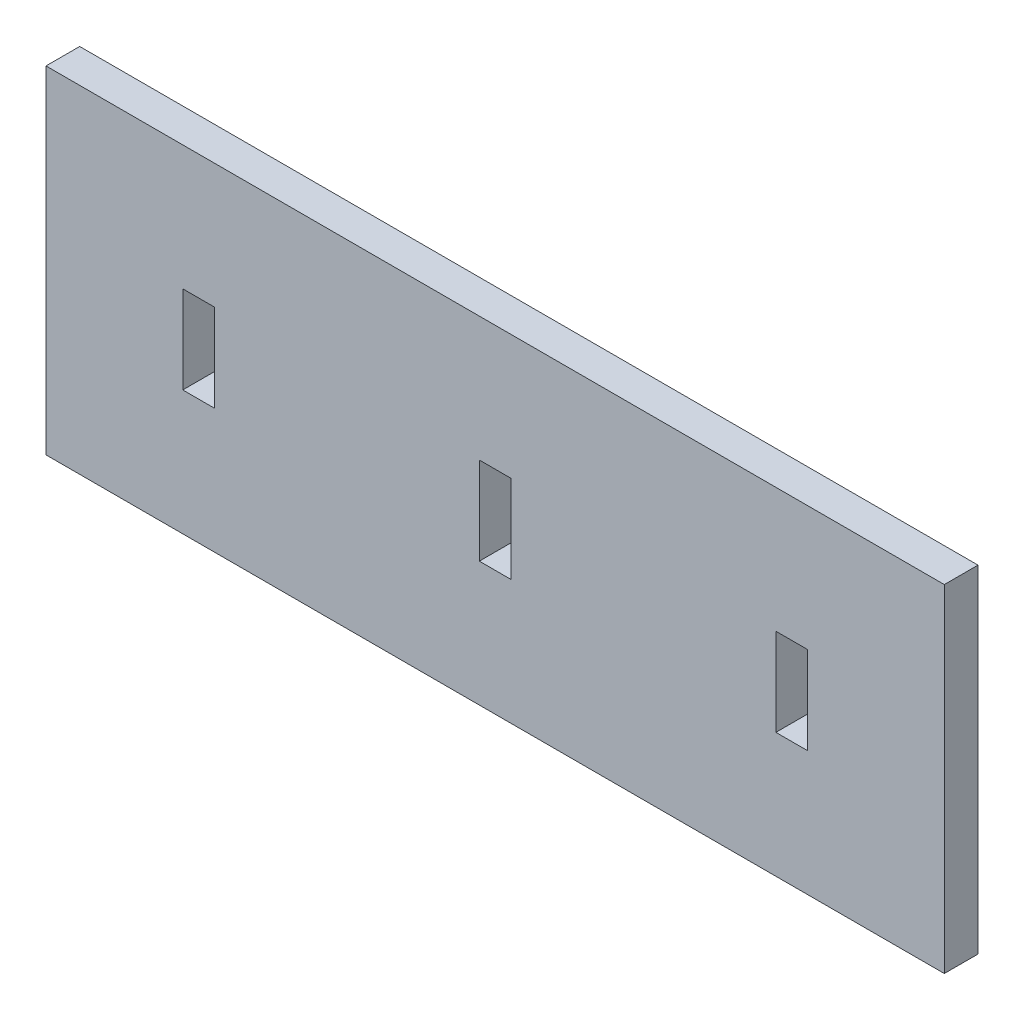
SolidWorks part; units mm, degrees
ref_plane "Front Plane" through (0, 0, 0) normal (0, 0, 1) x (1, 0, 0)
ref_plane "Top Plane" through (0, 0, 0) normal (0, 1, 0) x (1, 0, 0)
ref_plane "Right Plane" through (0, 0, 0) normal (1, 0, 0) x (0, 0, -1)
sketch "Sketch2" plane through (0, 0, 0) normal (0, 0, 1) x (1, 0, 0)
  line L0 (-26.41, 3.9) -> (26.41, 3.9) construction
  line L1 (-40, -15) -> (40, -15)
  line L2 (-40, -15) -> (-40, 15)
  line L3 (-40, 15) -> (40, 15)
  line L4 (40, -15) -> (40, 15)
  line L5 (-27.82, 3.9) -> (-25, 3.9)
  line L6 (-27.82, 3.9) -> (-27.82, -3.9)
  line L7 (-27.82, -3.9) -> (-25, -3.9)
  line L8 (-25, 3.9) -> (-25, -3.9)
  line L9 (25, 3.9) -> (27.82, 3.9)
  line L10 (25, 3.9) -> (25, -3.9)
  line L11 (25, -3.9) -> (27.82, -3.9)
  line L12 (27.82, 3.9) -> (27.82, -3.9)
  line L13 (-1.41, -3.9) -> (1.41, -3.9)
  line L14 (-1.41, -3.9) -> (-1.41, 3.9)
  line L15 (-1.41, 3.9) -> (1.41, 3.9)
  line L16 (1.41, -3.9) -> (1.41, 3.9)
  line L17 (-1.41, -3.9) -> (1.41, 3.9) construction
  line L18 (-1.41, 3.9) -> (1.41, -3.9) construction
  point P0 (0, 0)
  point P14 (0, -15)
  point P15 (40, 0)
  point P16 (25, 0)
  point P17 (-25, 0)
  point P18 (0, 0)
  point P25 (0, 3.9)
  point P26 (1.41, 3.4198)
  point P27 (25, 3.9)
  point P28 (26.41, 3.9)
  dimension "D1" = 2.82
  dimension "D2" = 80
  dimension "D3" = 30
  dimension "D4" = 7.8
  dimension "D5" = 50
extrude "Boss-Extrude1" add sketch "Sketch2" along normal blind 3
